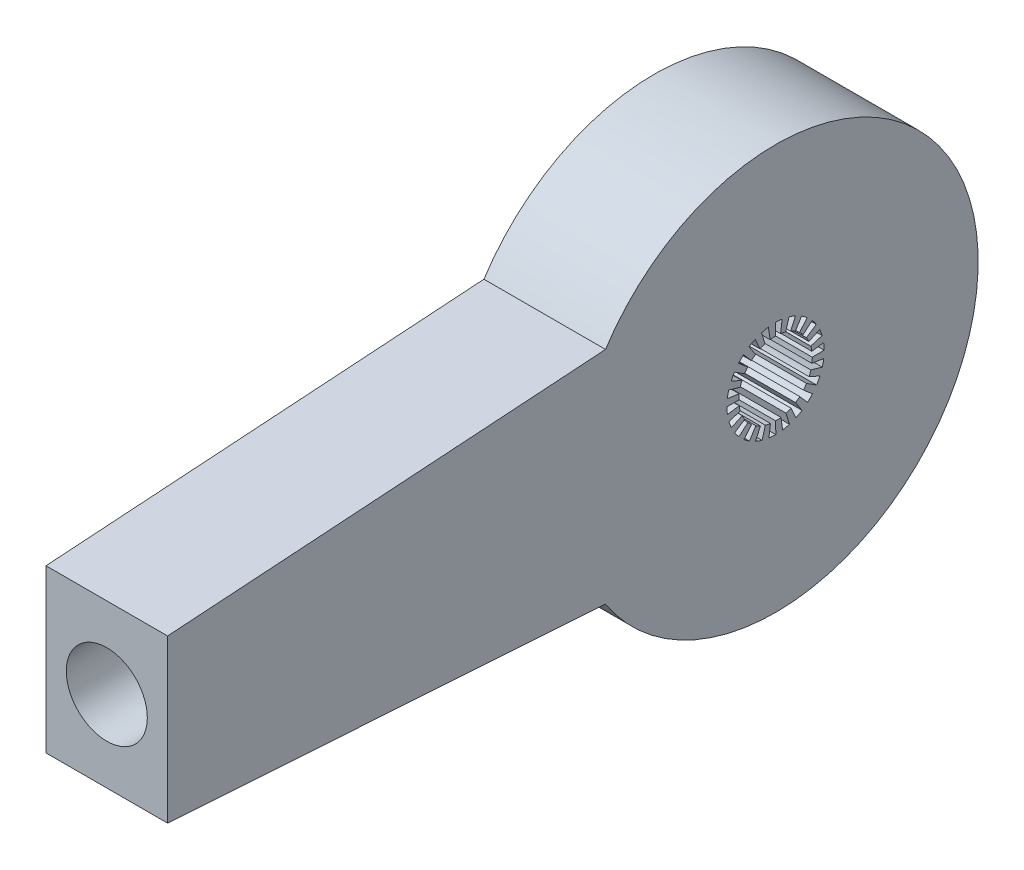
SolidWorks part; units mm, degrees
ref_plane "Front Plane" through (0, 0, 0) normal (0, 0, 1) x (1, 0, 0)
ref_plane "Top Plane" through (0, 0, 0) normal (0, 1, 0) x (1, 0, 0)
ref_plane "Right Plane" through (0, 0, 0) normal (1, 0, 0) x (0, 0, -1)
sketch "Sketch1" plane through (0, 0, 0) normal (1, 0, 0) x (0, 0, -1)
  line L0 (0, 15) -> (-75, 10)
  line L1 (-75, 10) -> (-75, -10)
  line L2 (-75, -10) -> (0, -15)
  circle A0 centre (0, 0) radius 6
  circle A1 centre (0, 0) radius 25
  arc A2 (-1.9912, -14.8673) -> (0, 15) centre (0, 0) ccw construction
  dimension "D1" = 30
  dimension "D3" = 50
  dimension "D4" = 12
  dimension "D2" = 75
  dimension "D5" = 20
  dimension "D6" = 10
extrude "Boss-Extrude1" add sketch "Sketch1" along normal blind 15
sketch "Sketch2" plane through (0, 0, 75) normal (0, 0, 1) x (1, 0, 0)
  line L0 (15, 10) -> (15, -10) construction
  circle A0 centre (7.5, 0) radius 5
  dimension "D2" = 10
  dimension "D1" = 7.5
extrude "Cut-Extrude1" cut sketch "Sketch2" against normal blind 30
sketch "Sketch4" plane through (15, 0, 0) normal (1, 0, 0) x (0, 0, -1)
  line L0 (0.6233, 4.4901) -> (0.8249, 5.943)
  line L3 (1.863, 4.1326) -> (2.4659, 5.4699)
  line L4 (1.2558, 4.3557) -> (1.6621, 5.7652)
  line L5 (2.4321, 3.8255) -> (3.219, 5.0634)
  line L6 (2.9519, 3.4404) -> (3.907, 4.5536)
  line L7 (3.4113, 2.9854) -> (4.5152, 3.9514)
  line L8 (3.8015, 2.4694) -> (5.0317, 3.2684)
  line L9 (4.1142, 1.9033) -> (5.4455, 2.5192)
  line L10 (4.3433, 1.2983) -> (5.7487, 1.7184)
  line L11 (4.4838, 0.6671) -> (5.9347, 0.883)
  line L12 (4.5331, 0.0221) -> (5.9999, 0.0292)
  line L13 (4.4901, -0.6231) -> (5.943, -0.8247)
  line L14 (4.3557, -1.2559) -> (5.7651, -1.6623)
  line L15 (4.1327, -1.8629) -> (5.47, -2.4657)
  line L16 (3.8254, -2.4322) -> (5.0633, -3.2192)
  line L17 (3.4404, -2.9517) -> (4.5537, -3.9069)
  line L18 (2.9852, -3.4114) -> (3.9512, -4.5153)
  line L19 (2.4695, -3.8015) -> (3.2686, -5.0315)
  line L20 (1.9032, -4.1143) -> (2.5191, -5.4456)
  line L21 (1.2985, -4.3432) -> (1.7186, -5.7486)
  line L22 (0.667, -4.4838) -> (0.8828, -5.9347)
  line L23 (0.0222, -4.5331) -> (0.0294, -5.9999)
  line L24 (-0.6233, -4.4901) -> (-0.8249, -5.943)
  line L25 (-1.2558, -4.3557) -> (-1.6621, -5.7652)
  line L26 (-1.863, -4.1326) -> (-2.4659, -5.4699)
  line L27 (-2.4321, -3.8255) -> (-3.219, -5.0634)
  line L28 (-2.9519, -3.4404) -> (-3.907, -4.5536)
  line L29 (-3.4113, -2.9854) -> (-4.5152, -3.9514)
  line L30 (-3.8015, -2.4694) -> (-5.0317, -3.2684)
  line L31 (-4.1142, -1.9033) -> (-5.4455, -2.5192)
  line L32 (-4.3433, -1.2983) -> (-5.7487, -1.7184)
  line L33 (-4.4838, -0.6671) -> (-5.9347, -0.883)
  line L34 (-4.5331, -0.0221) -> (-5.9999, -0.0292)
  line L35 (-4.4901, 0.6231) -> (-5.943, 0.8247)
  line L36 (-4.3557, 1.2559) -> (-5.7651, 1.6623)
  line L37 (-4.1327, 1.8629) -> (-5.47, 2.4657)
  line L38 (-3.8254, 2.4322) -> (-5.0633, 3.2192)
  line L39 (-3.4404, 2.9517) -> (-4.5537, 3.9069)
  line L40 (-2.9852, 3.4114) -> (-3.9512, 4.5153)
  line L41 (-2.4695, 3.8015) -> (-3.2686, 5.0315)
  line L42 (-1.9032, 4.1143) -> (-2.5191, 5.4456)
  line L43 (-1.2985, 4.3432) -> (-1.7186, 5.7486)
  line L44 (-0.667, 4.4838) -> (-0.8828, 5.9347)
  line L45 (-0.0222, 4.5331) -> (-0.0294, 5.9999)
  circle A0 centre (0, 0) radius 6 construction
  arc A1 (1.2558, 4.3557) -> (0.6233, 4.4901) centre (0, 0) ccw
  arc A2 (1.6621, 5.7652) -> (0.8249, 5.943) centre (0, 0) ccw
  arc A3 (3.219, 5.0634) -> (2.4659, 5.4699) centre (0, 0) ccw
  arc A4 (2.4321, 3.8255) -> (1.863, 4.1326) centre (0, 0) ccw
  arc A5 (4.5152, 3.9514) -> (3.907, 4.5536) centre (0, 0) ccw
  arc A6 (3.4113, 2.9854) -> (2.9519, 3.4404) centre (0, 0) ccw
  arc A7 (5.4455, 2.5192) -> (5.0317, 3.2684) centre (0, 0) ccw
  arc A8 (4.1142, 1.9033) -> (3.8015, 2.4694) centre (0, 0) ccw
  arc A9 (5.9347, 0.883) -> (5.7487, 1.7184) centre (0, 0) ccw
  arc A10 (4.4838, 0.6671) -> (4.3433, 1.2983) centre (0, 0) ccw
  arc A11 (5.943, -0.8247) -> (5.9999, 0.0292) centre (0, 0) ccw
  arc A12 (4.4901, -0.6231) -> (4.5331, 0.0221) centre (0, 0) ccw
  arc A13 (5.47, -2.4657) -> (5.7651, -1.6623) centre (0, 0) ccw
  arc A14 (4.1327, -1.8629) -> (4.3557, -1.2559) centre (0, 0) ccw
  arc A15 (4.5537, -3.9069) -> (5.0633, -3.2192) centre (0, 0) ccw
  arc A16 (3.4404, -2.9517) -> (3.8254, -2.4322) centre (0, 0) ccw
  arc A17 (3.2686, -5.0315) -> (3.9512, -4.5153) centre (0, 0) ccw
  arc A18 (2.4695, -3.8015) -> (2.9852, -3.4114) centre (0, 0) ccw
  arc A19 (1.7186, -5.7486) -> (2.5191, -5.4456) centre (0, 0) ccw
  arc A20 (1.2985, -4.3432) -> (1.9032, -4.1143) centre (0, 0) ccw
  arc A21 (0.0294, -5.9999) -> (0.8828, -5.9347) centre (0, 0) ccw
  arc A22 (0.0222, -4.5331) -> (0.667, -4.4838) centre (0, 0) ccw
  arc A23 (-1.6621, -5.7652) -> (-0.8249, -5.943) centre (0, 0) ccw
  arc A24 (-1.2558, -4.3557) -> (-0.6233, -4.4901) centre (0, 0) ccw
  arc A25 (-3.219, -5.0634) -> (-2.4659, -5.4699) centre (0, 0) ccw
  arc A26 (-2.4321, -3.8255) -> (-1.863, -4.1326) centre (0, 0) ccw
  arc A27 (-4.5152, -3.9514) -> (-3.907, -4.5536) centre (0, 0) ccw
  arc A28 (-3.4113, -2.9854) -> (-2.9519, -3.4404) centre (0, 0) ccw
  arc A29 (-5.4455, -2.5192) -> (-5.0317, -3.2684) centre (0, 0) ccw
  arc A30 (-4.1142, -1.9033) -> (-3.8015, -2.4694) centre (0, 0) ccw
  arc A31 (-5.9347, -0.883) -> (-5.7487, -1.7184) centre (0, 0) ccw
  arc A32 (-4.4838, -0.6671) -> (-4.3433, -1.2983) centre (0, 0) ccw
  arc A33 (-5.943, 0.8247) -> (-5.9999, -0.0292) centre (0, 0) ccw
  arc A34 (-4.4901, 0.6231) -> (-4.5331, -0.0221) centre (0, 0) ccw
  arc A35 (-5.47, 2.4657) -> (-5.7651, 1.6623) centre (0, 0) ccw
  arc A36 (-4.1327, 1.8629) -> (-4.3557, 1.2559) centre (0, 0) ccw
  arc A37 (-4.5537, 3.9069) -> (-5.0633, 3.2192) centre (0, 0) ccw
  arc A38 (-3.4404, 2.9517) -> (-3.8254, 2.4322) centre (0, 0) ccw
  arc A39 (-3.2686, 5.0315) -> (-3.9512, 4.5153) centre (0, 0) ccw
  arc A40 (-2.4695, 3.8015) -> (-2.9852, 3.4114) centre (0, 0) ccw
  arc A41 (-1.7186, 5.7486) -> (-2.5191, 5.4456) centre (0, 0) ccw
  arc A42 (-1.2985, 4.3432) -> (-1.9032, 4.1143) centre (0, 0) ccw
  arc A43 (-0.0294, 5.9999) -> (-0.8828, 5.9347) centre (0, 0) ccw
  arc A44 (-0.0222, 4.5331) -> (-0.667, 4.4838) centre (0, 0) ccw
  dimension "D1" = 22
  dimension "D2" = 8.18
extrude "Boss-Extrude2" add sketch "Sketch4" against normal up to surface (15 mm away) up to face at (0, 0, 36.494)
